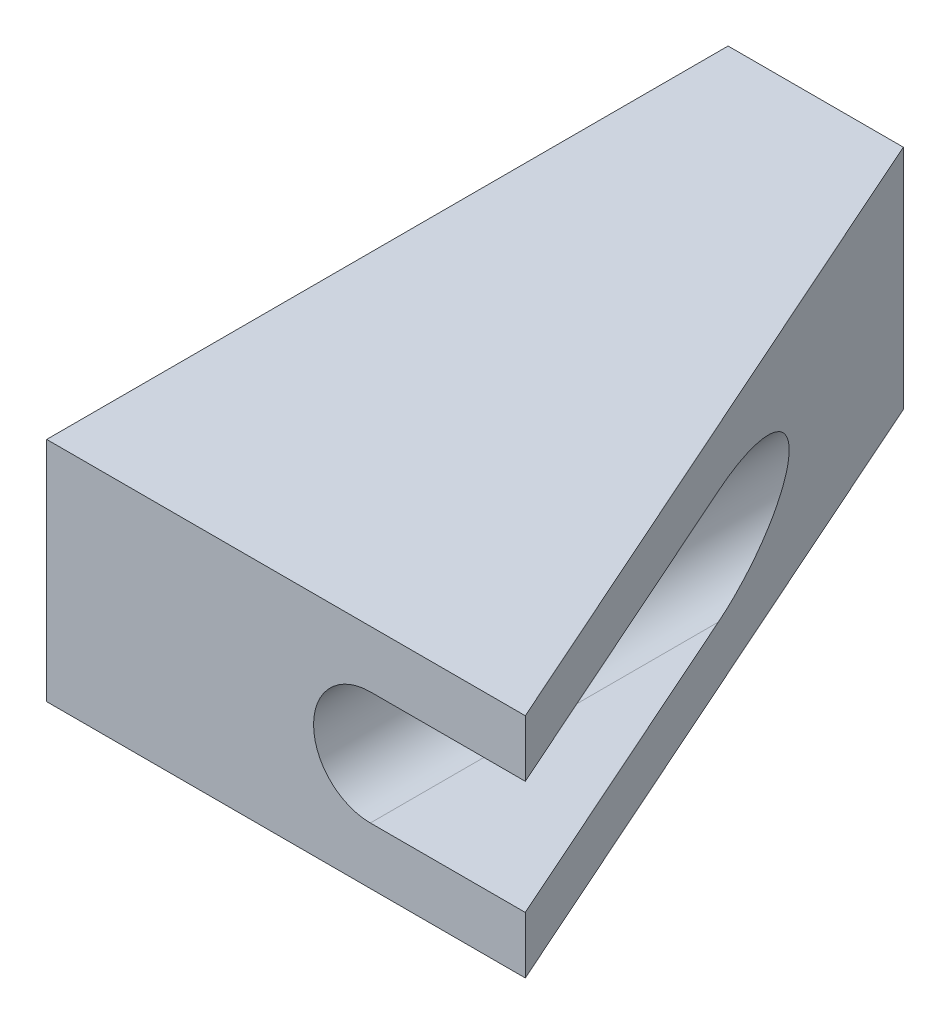
SolidWorks part; units mm, degrees
ref_plane "Спереди" through (0, 0, 0) normal (0, 0, 1) x (1, 0, 0)
ref_plane "Сверху" through (0, 0, 0) normal (0, 1, 0) x (1, 0, 0)
ref_plane "Справа" through (0, 0, 0) normal (1, 0, 0) x (0, 0, -1)
sketch "Эскиз1" plane through (0, 0, 0) normal (0, 1, 0) x (1, 0, 0)
  line L0 (0, 0) -> (0, 12)
  line L1 (0, 12) -> (3.086, 12)
  line L2 (3.086, 12) -> (8.4287, 0)
  line L3 (8.4287, 0) -> (0, 0)
  dimension "D1" = 12
  dimension "D2" = 24
  dimension "D3" = 7.7
extrude "Бобышка-Вытянуть1" add sketch "Эскиз1" along normal blind 4
sketch "Эскиз2" plane through (0, 0, 0) normal (0, 0, 1) x (1, 0, 0)
  line L0 (0, 4) -> (0, 0) construction
  line L1 (0, 4) -> (8.4287, 4) construction
  circle A0 centre (5.7, 2) radius 1
  dimension "D1" = 2
  dimension "D2" = 5.7
  dimension "D3" = 2
extrude "Вырез-Вытянуть1" cut sketch "Эскиз2" against normal through all
sketch "Эскиз3" plane through (0, 0, 0) normal (0, 0, 1) x (1, 0, 0)
  line L0 (5.7, 3) -> (8.4287, 3)
  line L1 (8.4287, 4) -> (8.4287, 0) construction
  line L2 (5.7, 1) -> (8.4287, 1)
  circle A0 centre (5.7, 2) radius 1 construction
  circle M1 centre (5.7, 2) radius 1
  line M3 (8.4287, 0) -> (8.4287, 4)
extrude "Вырез-Вытянуть2" cut sketch "Эскиз3" against normal through all contours L2 L0 M1 M3
